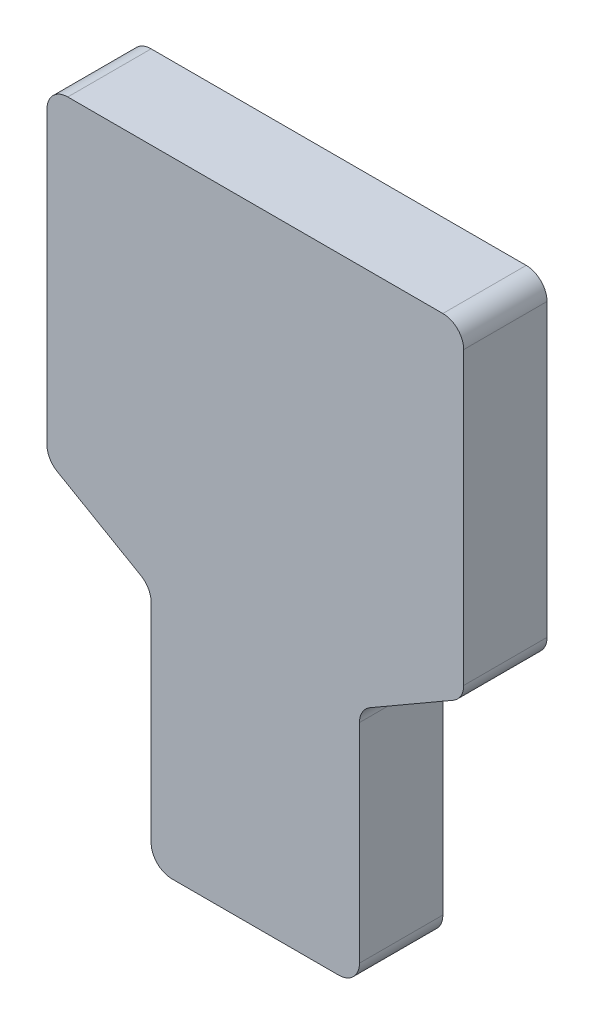
SolidWorks part; units mm, degrees
ref_plane "Plano frontal" through (0, 0, 0) normal (0, 0, 1) x (1, 0, 0)
ref_plane "Plano superior" through (0, 0, 0) normal (0, 1, 0) x (1, 0, 0)
ref_plane "Plano direito" through (0, 0, 0) normal (1, 0, 0) x (0, 0, -1)
sketch "Esboço1" plane through (0, 0, 0) normal (0, 0, 1) x (1, 0, 0)
  line L0 (-40, 0) -> (40, 0)
  line L1 (-50, 10) -> (-50, 110)
  line L2 (-55, 118.6603) -> (-95, 141.7543)
  line L3 (-100, 150.4145) -> (-100, 290)
  line L4 (-90, 300) -> (90, 300)
  line L5 (0, 300) -> (0, 0) construction
  line L6 (100, 150.4145) -> (100, 290)
  line L7 (55, 118.6603) -> (95, 141.7543)
  line L8 (50, 10) -> (50, 110)
  arc A0 (-100, 290) -> (-90, 300) centre (-90, 290) cw
  arc A1 (-95, 141.7543) -> (-100, 150.4145) centre (-90, 150.4145) cw
  arc A2 (-50, 110) -> (-55, 118.6603) centre (-60, 110) ccw
  arc A3 (-40, 0) -> (-50, 10) centre (-40, 10) cw
  arc A4 (40, 0) -> (50, 10) centre (40, 10) ccw
  arc A5 (50, 110) -> (55, 118.6603) centre (60, 110) cw
  arc A6 (95, 141.7543) -> (100, 150.4145) centre (90, 150.4145) ccw
  arc A7 (100, 290) -> (90, 300) centre (90, 290) ccw
  dimension "D1" = 10
  dimension "D2" = 100
  dimension "D3" = 300
  dimension "D4" = 50
  dimension "D5" = 100
  dimension "D6" = 60
extrude "Ressalto-extrusão1" add sketch "Esboço1" along normal mid plane 40
